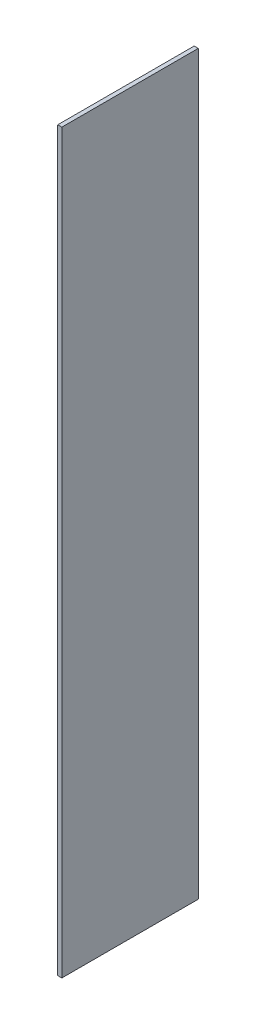
SolidWorks part; units mm, degrees
ref_plane "Front Plane" through (0, 0, 0) normal (0, 0, 1) x (1, 0, 0)
ref_plane "Top Plane" through (0, 0, 0) normal (0, 1, 0) x (1, 0, 0)
ref_plane "Right Plane" through (0, 0, 0) normal (1, 0, 0) x (0, 0, -1)
sketch "Sketch1" plane through (0, 0, 0) normal (0, 1, 0) x (1, 0, 0)
  line L1 (-0.75, 25) -> (0.75, 25)
  line L2 (-0.75, 25) -> (-0.75, -25)
  line L3 (-0.75, -25) -> (0.75, -25)
  line L4 (0.75, 25) -> (0.75, -25)
  line L5 (-0.75, 25) -> (0.75, -25) construction
  line L6 (-0.75, -25) -> (0.75, 25) construction
  point P0 (0, 0)
  dimension "D1" = 50
  dimension "D2" = 1.5
extrude "Boss-Extrude1" add sketch "Sketch1" along normal mid plane 270
